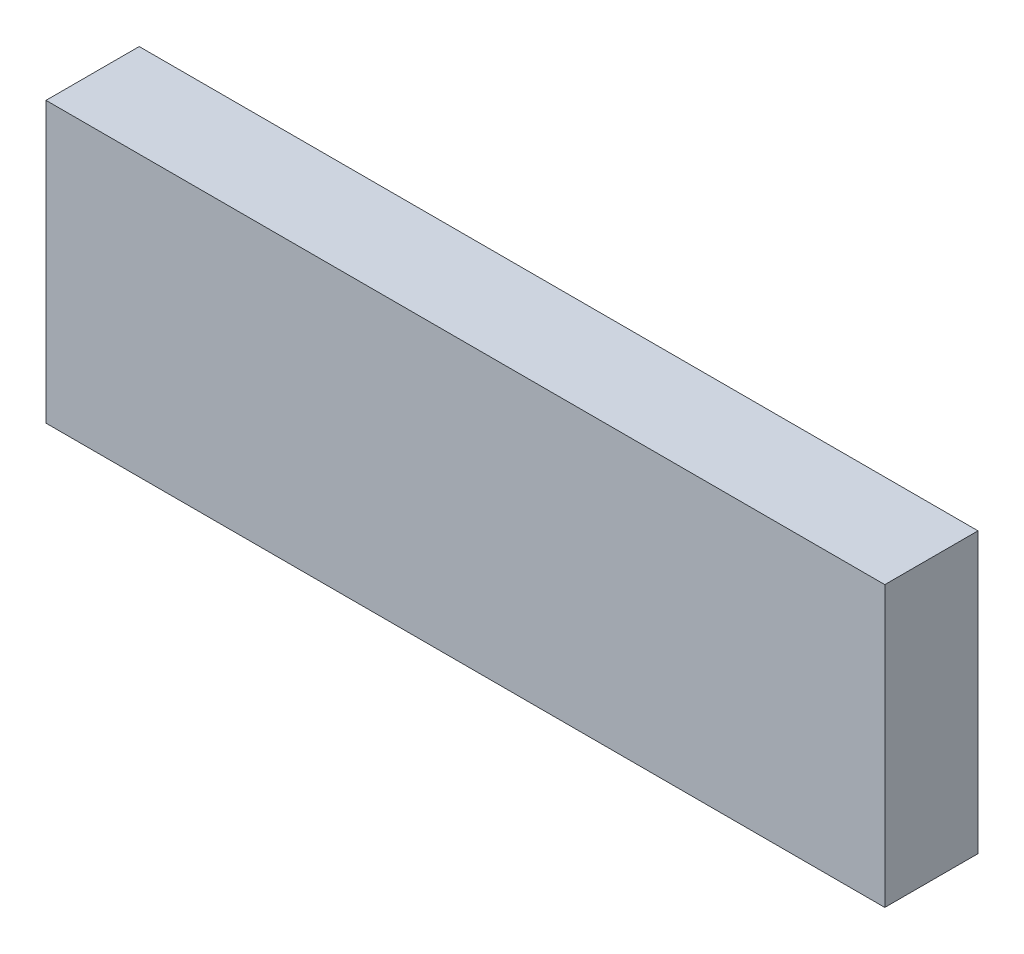
SolidWorks part; units mm, degrees
ref_plane "Front" through (0, 0, 0) normal (0, 0, 1) x (1, 0, 0)
ref_plane "Top" through (0, 0, 0) normal (0, 1, 0) x (1, 0, 0)
ref_plane "Right" through (0, 0, 0) normal (1, 0, 0) x (0, 0, -1)
sketch "Sketch1" plane through (0, 0, 0) normal (0, 0, 1) x (1, 0, 0)
  line L1 (-90, -30) -> (90, -30)
  line L2 (-90, -30) -> (-90, 30)
  line L3 (-90, 30) -> (90, 30)
  line L4 (90, -30) -> (90, 30)
  line L5 (-90, -30) -> (90, 30) construction
  line L6 (-90, 30) -> (90, -30) construction
  point P0 (0, 0)
  dimension "D1" = 60
  dimension "D2" = 180
extrude "Boss-Extrude1" add sketch "Sketch1" along normal blind 20
